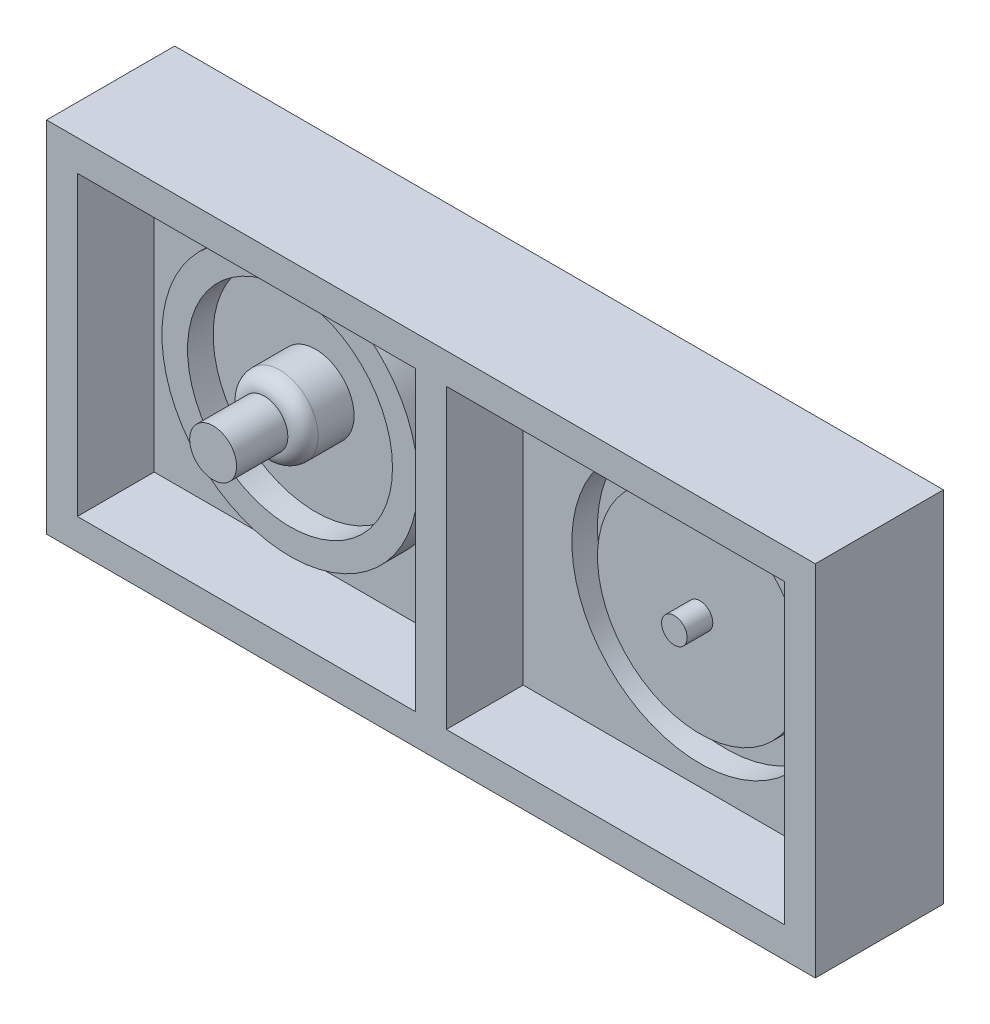
SolidWorks part; units mm, degrees
ref_plane "Plan de face" through (0, 0, 0) normal (0, 0, 1) x (1, 0, 0)
ref_plane "Plan de dessus" through (0, 0, 0) normal (0, 1, 0) x (1, 0, 0)
ref_plane "Plan de droite" through (0, 0, 0) normal (1, 0, 0) x (0, 0, -1)
sketch "Esquisse1" plane through (0, 0, 0) normal (0, 0, 1) x (1, 0, 0)
  line L1 (0, 0) -> (150, 0)
  line L2 (0, 0) -> (0, 70)
  line L3 (0, 70) -> (150, 70)
  line L4 (150, 0) -> (150, 70)
  dimension "D1" = 150
  dimension "D2" = 70
extrude "Boss.-Extru.1" add sketch "Esquisse1" along normal blind 25
sketch "Esquisse2" plane through (0, 0, 25) normal (0, 0, 1) x (1, 0, 0)
  line L0 (0, 70) -> (0, 0) construction
  line L1 (6, 64) -> (72, 64)
  line L2 (6, 64) -> (6, 6)
  line L3 (6, 6) -> (72, 6)
  line L4 (72, 64) -> (72, 6)
  line L5 (78, 64) -> (144, 64)
  line L6 (78, 64) -> (78, 6)
  line L7 (78, 6) -> (144, 6)
  line L8 (144, 64) -> (144, 6)
  line L9 (150, 0) -> (150, 70) construction
  line L10 (0, 0) -> (150, 0) construction
  line L11 (150, 70) -> (0, 70) construction
  point P10 (150, 35)
  dimension "D1" = 6
  dimension "D2" = 6
  dimension "D3" = 6
  dimension "D4" = 6
  dimension "D5" = 6
  dimension "D6" = 6
extrude "Enlèv. mat.-Extru.1" cut sketch "Esquisse2" against normal blind 15
sketch "Esquisse3" plane through (0, 0, 10) normal (0, 0, 1) x (1, 0, 0)
  line L1 (0, 0) -> (150, 0) construction
  line L4 (0, 70) -> (0, 0) construction
  circle A0 centre (37.5, 35) radius 25
  circle A1 centre (37.5, 35) radius 20
  dimension "D3" = 50
  dimension "D4" = 40
  dimension "D1" = 35
  dimension "D2" = 37.5
extrude "Boss.-Extru.2" add sketch "Esquisse3" along normal blind 5
sketch "Esquisse4" plane through (0, 0, 10) normal (0, 0, 1) x (1, 0, 0)
  line L0 (0, 0) -> (150, 0) construction
  line L1 (150, 0) -> (150, 70) construction
  circle A0 centre (112.5, 35) radius 25
  circle A1 centre (112.5, 35) radius 20
  dimension "D3" = 50
  dimension "D4" = 40
  dimension "D1" = 35
  dimension "D2" = 37.5
extrude "Enlèv. mat.-Extru.2" cut sketch "Esquisse4" against normal blind 5
sketch "Esquisse5" plane through (0, 0, 10) normal (0, 0, 1) x (1, 0, 0)
  circle A0 centre (37.5, 35) radius 7.5
  dimension "D1" = 15
extrude "Boss.-Extru.3" add sketch "Esquisse5" along normal blind 10
fillet "Congé2" radius 3 1 edges at (45, 35, 20)
sketch "Esquisse6" plane through (0, 0, 10) normal (0, 0, 1) x (1, 0, 0)
  circle A0 centre (112.5, 35) radius 2.5
  dimension "D1" = 5
extrude "Boss.-Extru.4" add sketch "Esquisse6" along normal blind 5
sketch "Esquisse7" plane through (0, 0, 20) normal (0, 0, 1) x (1, 0, 0)
  circle A0 centre (37.5, 35) radius 4.5753
extrude "Boss.-Extru.5" add sketch "Esquisse7" along normal blind 10
